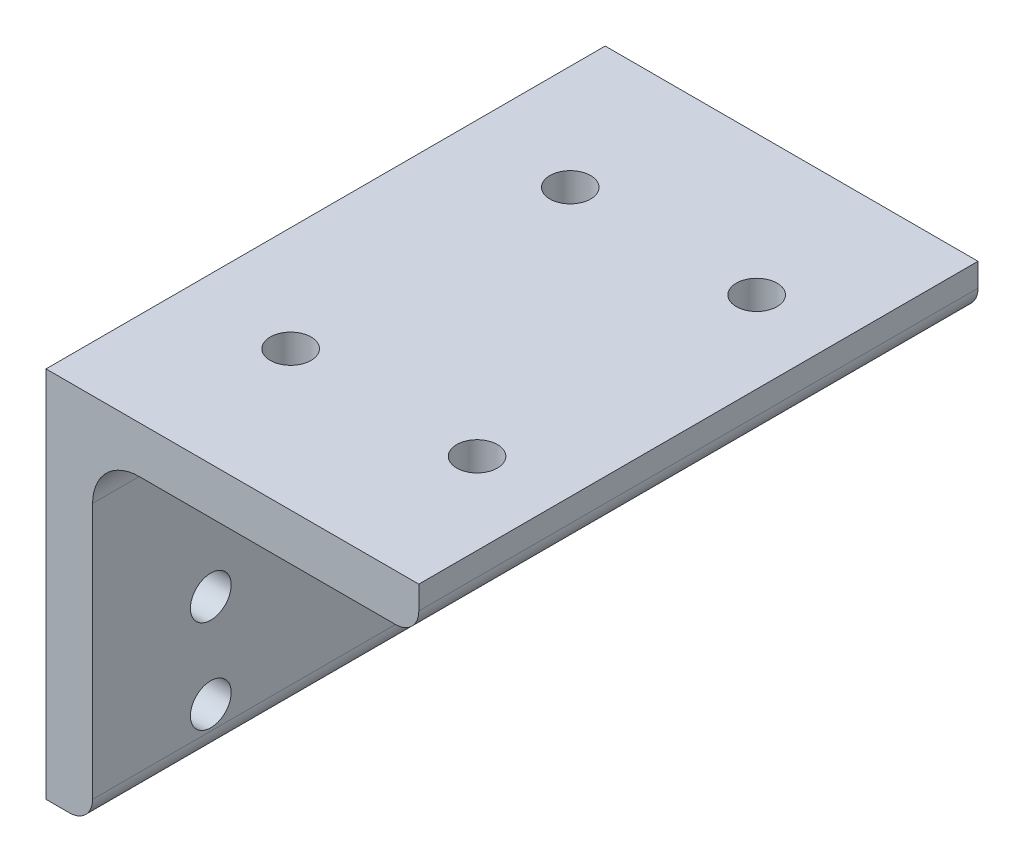
SolidWorks part; units mm, degrees
material "Alum 6061 (Default)"
ref_plane "Front Plane" through (0, 0, 0) normal (0, 0, 1) x (1, 0, 0)
ref_plane "Top Plane" through (0, 0, 0) normal (0, 1, 0) x (1, 0, 0)
ref_plane "Right Plane" through (0, 0, 0) normal (1, 0, 0) x (0, 0, -1)
sketch "Sketch1" plane through (0, 0, 0) normal (0, 0, 1) x (1, 0, 0)
  line L0 (0, 0) -> (50.8, 0)
  line L1 (0, 0) -> (0, -50.8)
  line L2 (6.35, -12.7) -> (6.35, -47.625)
  line L3 (12.7, -6.35) -> (47.625, -6.35)
  line L4 (50.8, 0) -> (50.8, -3.175)
  line L5 (0, -50.8) -> (3.175, -50.8)
  arc A0 (12.7, -6.35) -> (6.35, -12.7) centre (12.7, -12.7) ccw
  arc A1 (50.8, -3.175) -> (47.625, -6.35) centre (47.625, -3.175) cw
  arc A2 (6.35, -47.625) -> (3.175, -50.8) centre (3.175, -47.625) cw
  point P11 (50.8, -6.35)
  dimension "D4" = 6.35
  dimension "D5" = 3.175
  dimension "D1" = 50.8
  dimension "D2" = 50.8
  dimension "D3" = 6.35
extrude "Extrude1" add sketch "Sketch1" along normal mid plane 76.2
hole_wizard "7/32 (0.21875) Diameter Hole2" positions "Sketch3" profile "Sketch2" hole size "7/32" standard "Ansi Inch" end condition through all
sketch "Sketch3" plane through (-45.2437, 0, 38.1) normal (0, 1, 0) x (-1, 0, 0)
  line L0 (-84.9312, -19.05) -> (-59.5312, -19.05) construction
  line L1 (-59.5312, -19.05) -> (-59.5312, -57.15) construction
  line L2 (-59.5312, -57.15) -> (-84.9312, -57.15) construction
  line L3 (-84.9312, -57.15) -> (-84.9312, -19.05) construction
  line L4 (-45.2437, 0) -> (-45.2437, -76.2) construction
  line L7 (-84.9312, -38.1) -> (-59.5312, -38.1) construction
  point P0 (-84.9312, -19.05)
  point P1 (-84.9312, -57.15)
  point P3 (-59.5312, -57.15)
  point P5 (-59.5312, -19.05)
  dimension "D1" = 14.2875
  dimension "D2" = 25.4
  dimension "D3" = 38.1
sketch "Sketch2" plane through (39.6875, 0, 19.05) normal (1, 0, 0) x (0, 0, 1)
  line L0 (0, 0) -> (0, 50.8)
  line L1 (0, 50.8) -> (2.7781, 50.8)
  line L2 (2.7781, 50.8) -> (2.7781, 0)
  line L5 (2.7781, 0) -> (0, 0)
  line L11 (0, -6.35) -> (0, 107.95) construction
  dimension "Thru Hole Dia." = 5.5562
  dimension "Thru Hole Depth" = 50.8
hole_wizard "7/32 (0.21875) Diameter Hole3" positions "Sketch5" profile "Sketch4" hole size "7/32" standard "ANSI Inch" end condition through all
sketch "Sketch5" plane through (6.35, 0, 0) normal (1, 0, 0) x (0, 0, -1)
  line L0 (-21.9964, -15.875) -> (21.9964, -15.875) construction
  line L1 (21.9964, -15.875) -> (21.9964, -44.45) construction
  line L2 (21.9964, -44.45) -> (-21.9964, -44.45) construction
  line L3 (-21.9964, -44.45) -> (-21.9964, -15.875) construction
  line L4 (-38.1, 0) -> (38.1, 0) construction
  line L5 (38.1, -47.625) -> (38.1, -12.7) construction
  line L7 (-38.1, -50.8) -> (38.1, -50.8) construction
  point P0 (-21.9964, -15.875)
  point P1 (21.9964, -15.875)
  point P3 (21.9964, -44.45)
  point P5 (-21.9964, -44.45)
  point P24 (-21.9964, -31.75)
  point P26 (21.9964, -31.75)
  dimension "D1" = 15.875
  dimension "D2" = 44.45
  dimension "D3" = 16.1036
  dimension "D4" = 60.0964
  dimension "D5" = 19.05
sketch "Sketch4" plane through (6.35, -15.875, 21.9964) normal (0, 1, 0) x (0, 0, -1)
  line L0 (0, 0) -> (0, 6.35)
  line L1 (0, 6.35) -> (2.7781, 6.35)
  line L2 (2.7781, 6.35) -> (2.7781, 0)
  line L5 (2.7781, 0) -> (0, 0)
  line L11 (0, -6.35) -> (0, 107.95) construction
  dimension "Thru Hole Dia." = 5.5562
  dimension "Thru Hole Depth" = 6.35
ref_plane "Plane1" through (0, -15.875, 0) normal (0, 1, 0) x (-1, 0, 0)
sketch "Sketch6" plane through (0, -15.875, 0) normal (0, 1, 0) x (-1, 0, 0)
  circle A0 centre (-14.2875, 19.05) radius 6.35
  circle A1 centre (-14.2875, -19.05) radius 6.35
  dimension "D1" = 12.7
extrude "Cut-Extrude1" cut sketch "Sketch6" along normal up to surface (9.525 mm away) up to face at (39.6875, -6.35, 21.8281)
